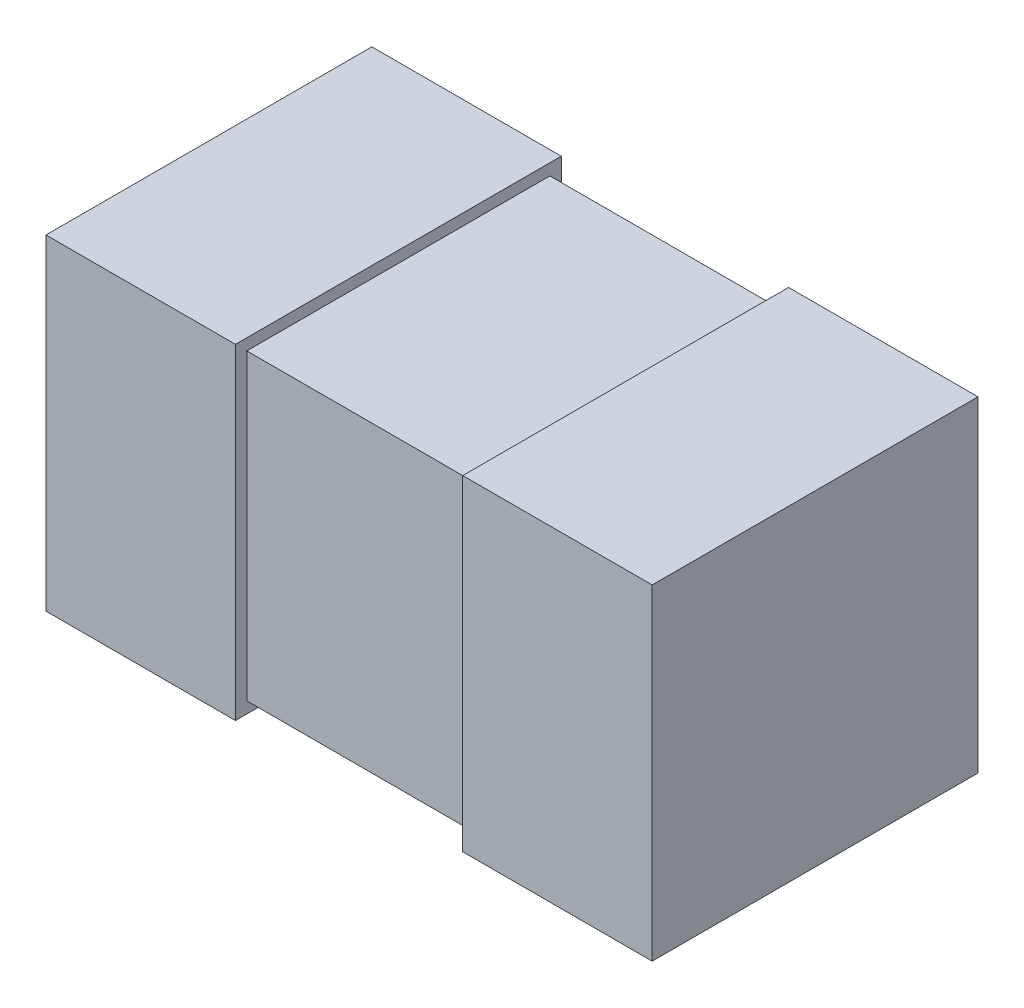
SolidWorks part; units mm, degrees
ref_plane "Front Plane" through (0, 0, 0) normal (0, 0, 1) x (1, 0, 0)
ref_plane "Top Plane" through (0, 0, 0) normal (0, 1, 0) x (1, 0, 0)
ref_plane "Right Plane" through (0, 0, 0) normal (1, 0, 0) x (0, 0, -1)
sketch "Sketch1" plane through (0, 0, 0) normal (0, 1, 0) x (1, 0, 0)
  line L1 (-0.8, 0.4) -> (0.8, 0.4)
  line L2 (-0.8, 0.4) -> (-0.8, -0.4)
  line L3 (-0.8, -0.4) -> (0.8, -0.4)
  line L4 (0.8, 0.4) -> (0.8, -0.4)
  point P4 (0, 0.4)
  point P6 (0.8, 0)
  dimension "D1" = 0.8
  dimension "D2" = 1.6
extrude "Extrude1" add sketch "Sketch1" along normal blind 0.8
sketch "Sketch2" plane through (0, 0, 0) normal (0, 0, 1) x (1, 0, 0)
  line L0 (-0.8, 0.8) -> (-0.8, 0) construction
  line L1 (-0.3, 0.83) -> (-0.8, 0.83)
  line L2 (-0.3, 0.83) -> (-0.3, -0.03)
  line L3 (-0.3, -0.03) -> (-0.8, -0.03)
  line L4 (-0.8, 0.83) -> (-0.8, -0.03)
  line L5 (-0.8, 0.8) -> (0.8, 0.8) construction
  line L6 (-0.8, 0) -> (0.8, 0) construction
  line L7 (0, 0) -> (0, -0.3575) construction
  line L8 (0.8, 0.83) -> (0.8, -0.03)
  line L9 (0.3, -0.03) -> (0.8, -0.03)
  line L10 (0.3, 0.83) -> (0.3, -0.03)
  line L11 (0.3, 0.83) -> (0.8, 0.83)
  dimension "D1" = 0.5
  dimension "D2" = 0.03
  dimension "D3" = 0.03
extrude "Extrude2" add sketch "Sketch2" along normal offset from surface 0.03 and the other way offset from surface (0.43 mm away) 0.03 up to face at (0, 0.4, 0.4) offset beyond the face yes other way up to face at (0, 0.4, -0.4)
ref_plane "Board Plane" through (0, -0.03, 0) normal (0, 1, 0) x (-1, 0, 0)
sketch "Component_Outline" plane through (0, -0.03, 0) normal (0, 1, 0) x (-1, 0, 0)
  line L0 (-0.3, 0.43) -> (-0.8, 0.43)
  line L1 (0.8, 0.43) -> (0.3, 0.43)
  line L2 (0.8, 0.43) -> (0.8, -0.43)
  line L3 (0.8, -0.43) -> (0.3, -0.43)
  line L4 (-0.8, 0.43) -> (-0.8, -0.43)
  line L5 (0.3, -0.4) -> (-0.3, -0.4)
  line L6 (0.3, -0.4) -> (0.3, -0.43)
  line L8 (-0.3, -0.4) -> (-0.3, -0.43)
  line L9 (-0.3, -0.43) -> (-0.8, -0.43)
  line L10 (0.3, 0.43) -> (0.3, 0.4)
  line L11 (0.3, 0.4) -> (-0.3, 0.4)
  line L12 (-0.3, 0.43) -> (-0.3, 0.4)
